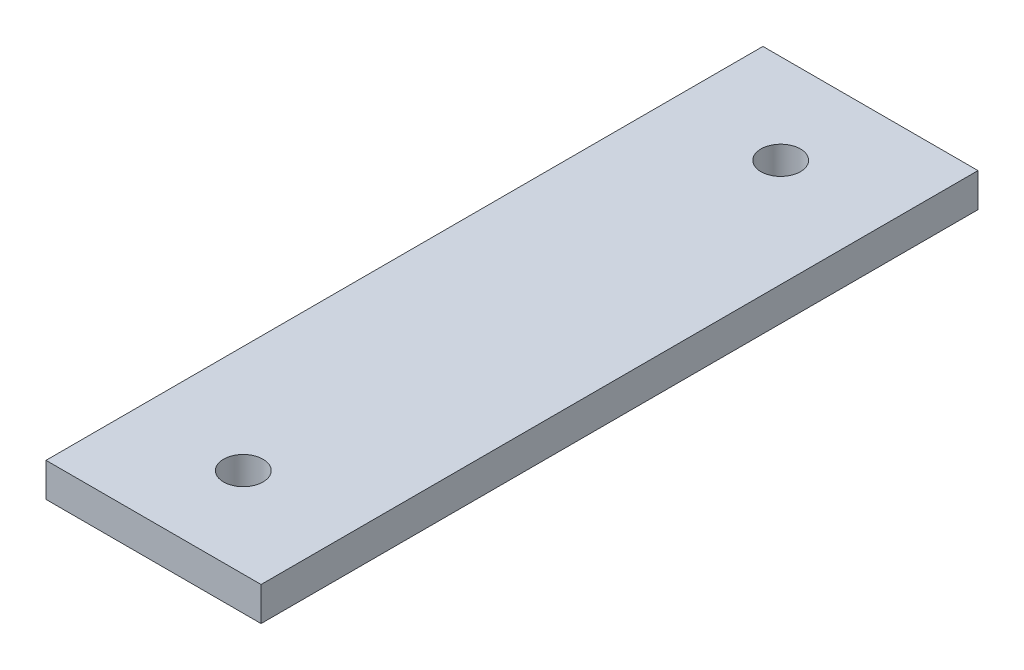
SolidWorks part; units mm, degrees
ref_plane "Front Plane" through (0, 0, 0) normal (0, 0, 1) x (1, 0, 0)
ref_plane "Top Plane" through (0, 0, 0) normal (0, 1, 0) x (1, 0, 0)
ref_plane "Right Plane" through (0, 0, 0) normal (1, 0, 0) x (0, 0, -1)
sketch "Sketch1" plane through (0, 0, 0) normal (0, 1, 0) x (1, 0, 0)
  line L1 (-12.7, -102) -> (25.4, -102)
  line L2 (-12.7, -102) -> (-12.7, 25)
  line L3 (-12.7, 25) -> (25.4, 25)
  line L4 (25.4, -102) -> (25.4, 25)
  point P4 (6.35, -102)
  point P5 (0, 0)
  dimension "D1" = 127
  dimension "D2" = 38.1
extrude "Boss-Extrude1" add sketch "Sketch1" along normal blind 6
sketch "Sketch2" plane through (0, 6, 0) normal (0, 1, 0) x (1, 0, 0)
  line L0 (6.35, 25) -> (6.35, -102) construction
  line L1 (25.4, 25) -> (-12.7, 25) construction
  line L2 (-12.7, -102) -> (25.4, -102) construction
  line L3 (25.4, -38.5) -> (-12.7, -38.5) construction
  line L4 (25.4, -102) -> (25.4, 25) construction
  line L5 (-12.7, 25) -> (-12.7, -102) construction
  circle A0 centre (6.35, 9.1) radius 3.5
  circle A1 centre (6.35, -86.1) radius 3.5
  dimension "D1" = 7
  dimension "D2" = 47.6
extrude "Cut-Extrude1" cut sketch "Sketch2" against normal through all
